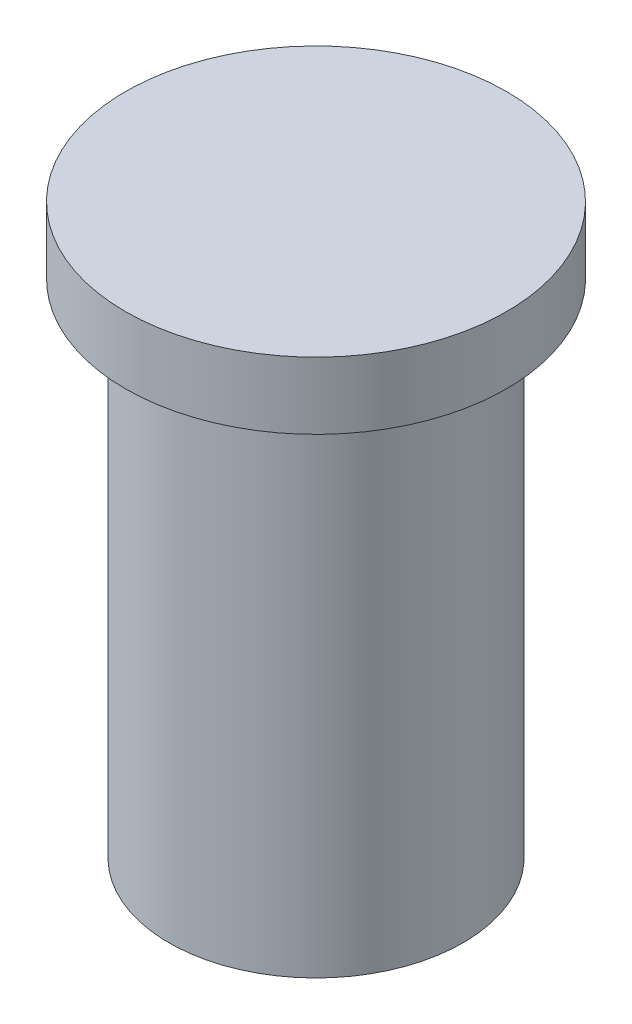
SolidWorks part; units mm, degrees
ref_plane "Front Plane" through (0, 0, 0) normal (0, 0, 1) x (1, 0, 0)
ref_plane "Top Plane" through (0, 0, 0) normal (0, 1, 0) x (1, 0, 0)
ref_plane "Right Plane" through (0, 0, 0) normal (1, 0, 0) x (0, 0, -1)
sketch "Sketch1" plane through (0, 0, 0) normal (0, 0, 1) x (1, 0, 0)
  line L0 (0, 0) -> (0, 78.4474) construction
  line L1 (0, 0) -> (22, 0)
  line L2 (22, 0) -> (22, 75)
  line L3 (22, 75) -> (28.5, 75)
  line L4 (28.5, 75) -> (28.5, 85)
  line L5 (28.5, 85) -> (0, 85)
  line L6 (0, 85) -> (0, 0)
  dimension "D1" = 44
  dimension "D2" = 57
  dimension "D3" = 85
  dimension "D4" = 75
revolve "Revolve1" add sketch "Sketch1" angle 360 about L0
